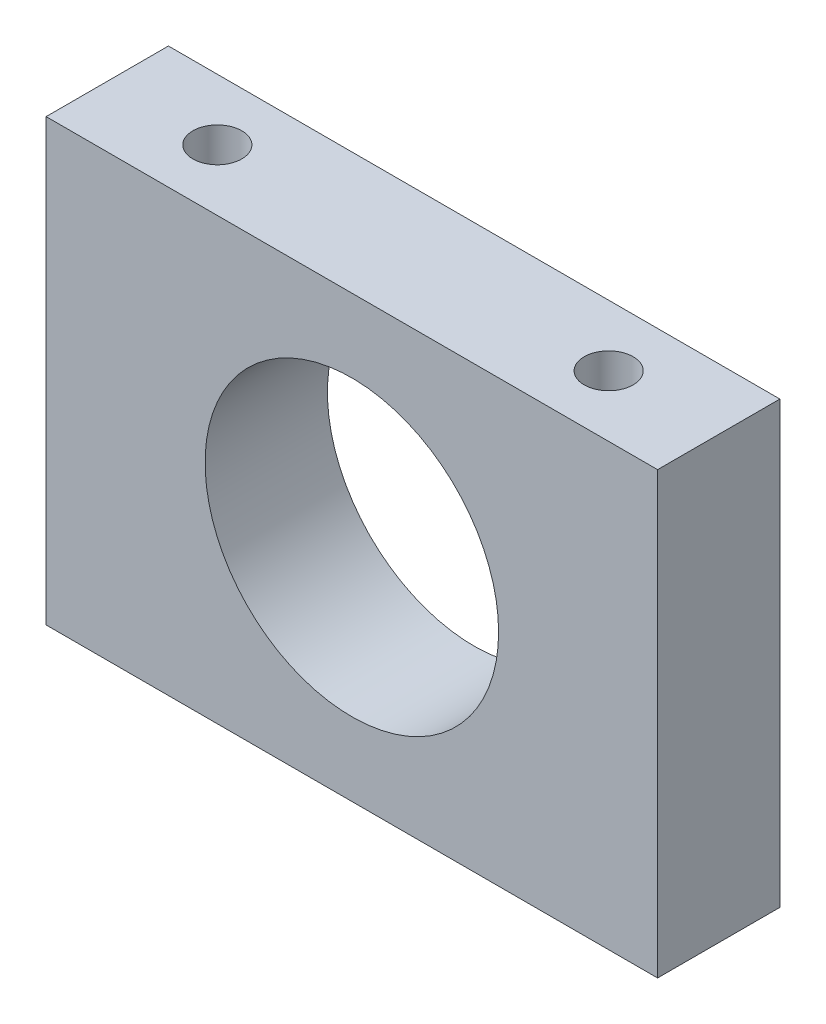
SolidWorks part; units mm, degrees
ref_plane "Plan de face" through (0, 0, 0) normal (0, 0, 1) x (1, 0, 0)
ref_plane "Plan de dessus" through (0, 0, 0) normal (0, 1, 0) x (1, 0, 0)
ref_plane "Plan de droite" through (0, 0, 0) normal (1, 0, 0) x (0, 0, -1)
sketch "Esquisse1" plane through (0, 0, 0) normal (0, 0, 1) x (1, 0, 0)
  line L1 (-12.5, 9) -> (12.5, 9)
  line L2 (-12.5, 9) -> (-12.5, -9)
  line L3 (-12.5, -9) -> (12.5, -9)
  line L4 (12.5, 9) -> (12.5, -9)
  circle A0 centre (0, 0) radius 6
  dimension "D1" = 9
  dimension "D2" = 18
  dimension "D3" = 25
  dimension "D4" = 12.5
extrude "Boss.-Extru.1" add sketch "Esquisse1" along normal blind 5
sketch "Esquisse2" plane through (0, 9, 0) normal (0, 1, 0) x (1, 0, 0)
  line L0 (12.5, 0) -> (-12.5, 0) construction
  circle A0 centre (-8, -2.5) radius 1
  circle A1 centre (8, -2.5) radius 1
  dimension "D5" = 2
  dimension "D6" = 2
  dimension "D1" = 2.5
  dimension "D2" = 2.5
  dimension "D3" = 8
  dimension "D4" = 8
extrude "Enlèv. mat.-Extru.1" cut sketch "Esquisse2" against normal blind 15
